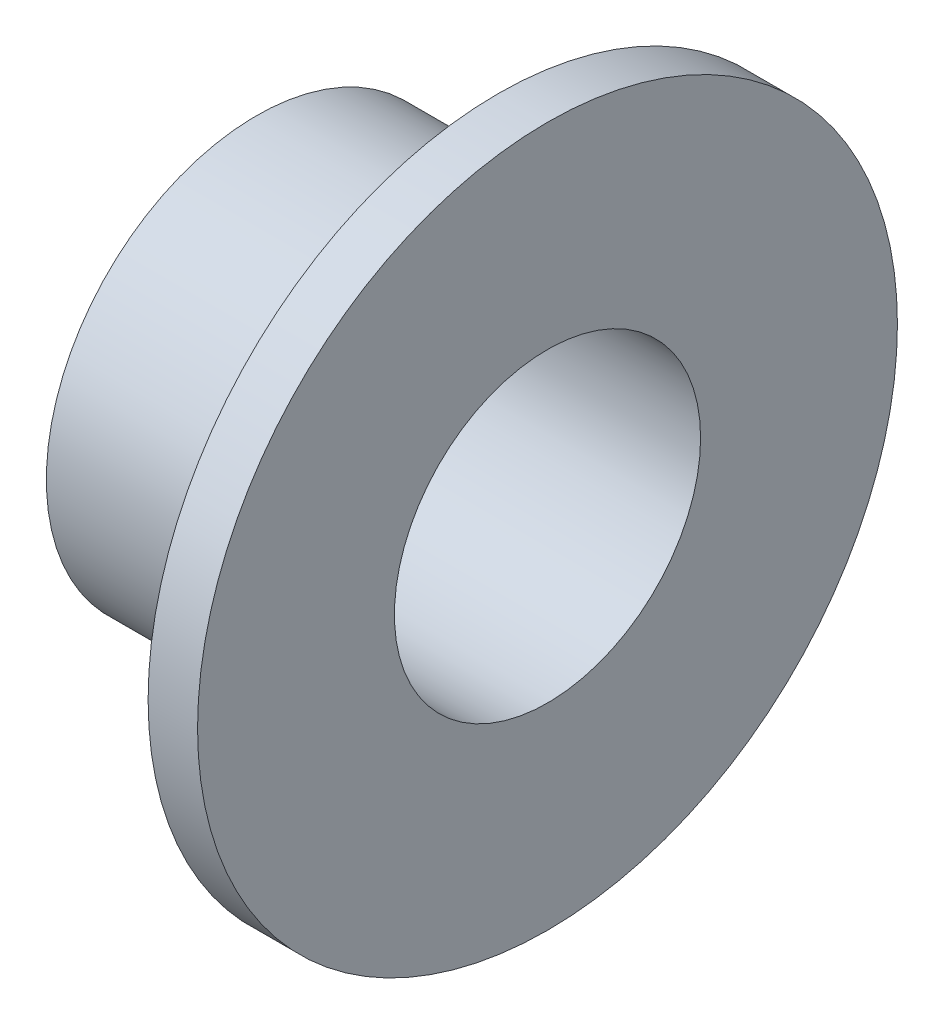
SolidWorks part; units mm, degrees
ref_plane "Front Plane" through (0, 0, 0) normal (0, 0, 1) x (1, 0, 0)
ref_plane "Top Plane" through (0, 0, 0) normal (0, 1, 0) x (1, 0, 0)
ref_plane "Right Plane" through (0, 0, 0) normal (1, 0, 0) x (0, 0, -1)
sketch "Sketch1" plane through (0, 0, 0) normal (0, 1, 0) x (1, 0, 0)
  line L0 (0, 2.0447) -> (0, 4.6736)
  line L1 (0, 4.6736) -> (-0.6604, 4.6736)
  line L2 (-0.6604, 4.6736) -> (-0.6604, 2.8067)
  line L3 (-0.6604, 2.8067) -> (-3.8862, 2.8067)
  line L4 (-3.8862, 2.8067) -> (-3.8862, 2.0447)
  line L5 (-3.8862, 2.0447) -> (0, 2.0447)
  line L6 (0, 0) -> (-33.5327, 0) construction
  dimension "D1" = 4.0894
  dimension "D2" = 5.6134
  dimension "D3" = 9.3472
  dimension "D4" = 0.6604
  dimension "D5" = 3.8862
revolve "Revolve1" add sketch "Sketch1" angle 360 about L6
